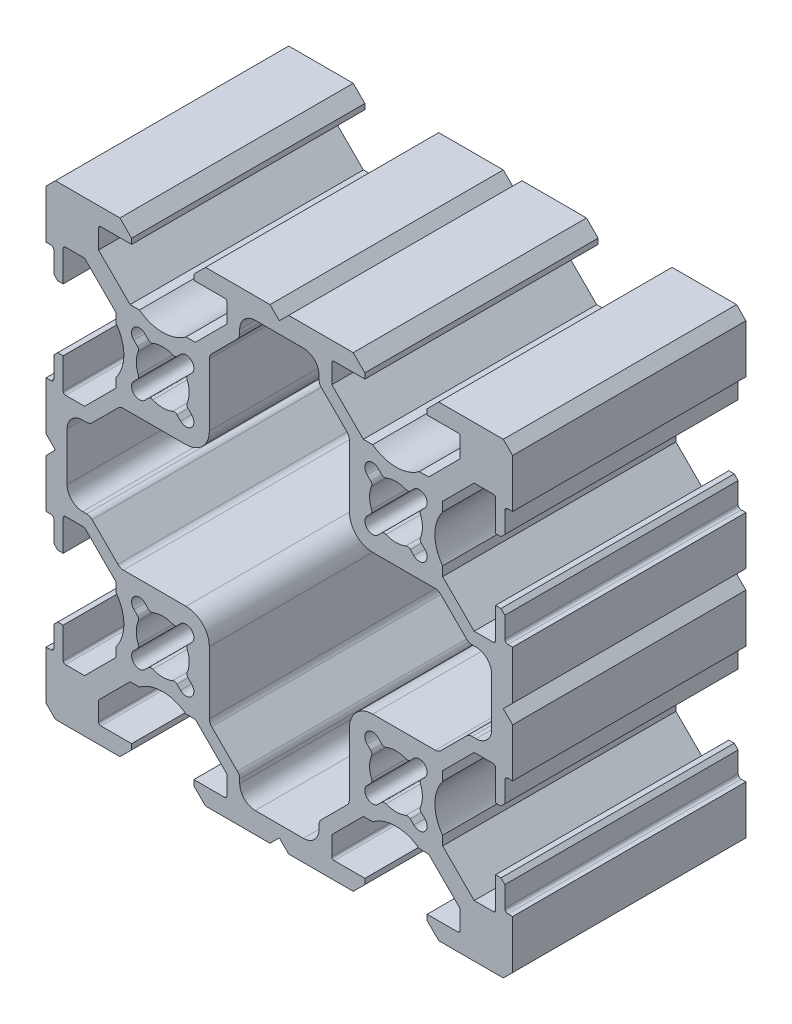
SolidWorks part; units mm, degrees
material "АД31Т ГОСТ 4784-97"
ref_plane "Спереди(Плоскость XY)" through (0, 0, 0) normal (0, 0, 1) x (1, 0, 0)
ref_plane "Сверху(Плоскость XZ)" through (0, 0, 0) normal (0, 1, 0) x (1, 0, 0)
ref_plane "Справа(Плоскость ZY)" through (0, 0, 0) normal (1, 0, 0) x (0, 0, -1)
sketch "Эскиз1" plane through (0, 0, 0) normal (0, 0, 1) x (1, 0, 0)
  line B0 (-19.6151, -16.8385) -> (-20.0747, -17.2981)
  line B1 (-20.0747, -12.7019) -> (-19.6151, -13.1615)
  line B2 (-18.2009, -11.7473) -> (-18.6605, -11.2877)
  line B3 (-14.0643, -11.2877) -> (-14.5239, -11.7473)
  line B4 (-13.1097, -13.1615) -> (-12.6501, -12.7019)
  line B5 (-12.6501, -17.2981) -> (-13.1097, -16.8385)
  line B6 (-14.5239, -18.2527) -> (-14.0643, -18.7123)
  line B7 (-18.6605, -18.7123) -> (-18.2009, -18.2527)
  line B8 (9.9253, -12.7019) -> (10.3849, -13.1615)
  line B9 (11.7991, -11.7473) -> (11.3395, -11.2877)
  line B10 (15.9357, -11.2877) -> (15.4761, -11.7473)
  line B11 (16.8903, -13.1615) -> (17.3499, -12.7019)
  line B12 (17.3499, -17.2981) -> (16.8903, -16.8385)
  line B13 (15.4761, -18.2527) -> (15.9357, -18.7123)
  line B14 (11.3395, -18.7123) -> (11.7991, -18.2527)
  line B15 (10.3849, -16.8385) -> (9.9253, -17.2981)
  line B16 (10.3849, 13.1615) -> (9.9253, 12.7019)
  line B17 (9.9253, 17.2981) -> (10.3849, 16.8385)
  line B18 (11.7991, 18.2527) -> (11.3395, 18.7123)
  line B19 (15.9357, 18.7123) -> (15.4761, 18.2527)
  line B20 (16.8903, 16.8385) -> (17.3499, 17.2981)
  line B21 (17.3499, 12.7019) -> (16.8903, 13.1615)
  line B22 (15.4761, 11.7473) -> (15.9357, 11.2877)
  line B23 (11.3395, 11.2877) -> (11.7991, 11.7473)
  line B24 (-18.2009, 18.2527) -> (-18.6605, 18.7123)
  line B25 (-14.0643, 18.7123) -> (-14.5239, 18.2527)
  line B26 (-13.1097, 16.8385) -> (-12.6501, 17.2981)
  line B27 (-12.6501, 12.7019) -> (-13.1097, 13.1615)
  line B28 (-14.5239, 11.7473) -> (-14.0643, 11.2877)
  line B29 (-18.6605, 11.2877) -> (-18.2009, 11.7473)
  line B30 (-19.6151, 13.1615) -> (-20.0747, 12.7019)
  line B31 (-20.0747, 17.2981) -> (-19.6151, 16.8385)
  line B32 (26.4376, 19) -> (27.1376, 19)
  line B33 (27.1376, 19) -> (27.6376, 19.5)
  line B34 (27.6376, 19.5) -> (27.6376, 22.15)
  line B35 (28.0376, 22.55) -> (28.6376, 22.55)
  line B36 (28.6376, 22.55) -> (28.6376, 28.8)
  line B37 (28.6376, 28.8) -> (27.4376, 30)
  line B38 (27.4376, 30) -> (19.1376, 30)
  line B39 (19.1376, 30) -> (17.6376, 28.5)
  line B40 (17.6376, 28.5) -> (17.6376, 27.8)
  line B41 (17.6376, 27.8) -> (21.5876, 27.8)
  line B42 (21.8876, 27.5) -> (21.8876, 25.0531)
  line B43 (21.8876, 25.0531) -> (17.8345, 21)
  line B44 (17.8345, 21) -> (16.6376, 21)
  line B45 (10.6376, 21) -> (9.4407, 21)
  line B46 (9.4407, 21) -> (5.3876, 25.0531)
  line B47 (5.3876, 25.0531) -> (5.3876, 27.5)
  line B48 (5.6876, 27.8) -> (9.6376, 27.8)
  line B49 (9.6376, 27.8) -> (9.6376, 28.5)
  line B50 (9.6376, 28.5) -> (8.1376, 30)
  line B51 (8.1376, 30) -> (-0.1624, 30)
  line B52 (-0.1624, 30) -> (-1.3624, 28.8)
  line B53 (-1.3624, 28.8) -> (-2.5624, 30)
  line B54 (-2.5624, 30) -> (-10.8624, 30)
  line B55 (-10.8624, 30) -> (-12.3624, 28.5)
  line B56 (-12.3624, 28.5) -> (-12.3624, 27.8)
  line B57 (-12.3624, 27.8) -> (-8.4124, 27.8)
  line B58 (-8.1124, 27.5) -> (-8.1124, 25.0531)
  line B59 (-8.1124, 25.0531) -> (-12.1655, 21)
  line B60 (-12.1655, 21) -> (-13.3624, 21)
  line B61 (-19.3624, 21) -> (-20.5593, 21)
  line B62 (-20.5593, 21) -> (-24.6124, 25.0531)
  line B63 (-24.6124, 25.0531) -> (-24.6124, 27.5)
  line B64 (-24.3124, 27.8) -> (-20.3624, 27.8)
  line B65 (-20.3624, 27.8) -> (-20.3624, 28.5)
  line B66 (-20.3624, 28.5) -> (-21.8624, 30)
  line B67 (-21.8624, 30) -> (-30.1624, 30)
  line B68 (-30.1624, 30) -> (-31.3624, 28.8)
  line B69 (-31.3624, 28.8) -> (-31.3624, 22.55)
  line B70 (-31.3624, 22.55) -> (-30.7624, 22.55)
  line B71 (-30.3624, 22.15) -> (-30.3624, 19.5)
  line B72 (-30.3624, 19.5) -> (-29.8624, 19)
  line B73 (-29.8624, 19) -> (-29.1624, 19)
  line B74 (-29.1624, 19) -> (-29.1624, 22.95)
  line B75 (-28.8624, 23.25) -> (-26.4155, 23.25)
  line B76 (-26.4155, 23.25) -> (-22.3624, 19.1969)
  line B77 (-22.3624, 19.1969) -> (-22.3624, 18)
  line B78 (-22.3624, 12) -> (-22.3624, 10.8031)
  line B79 (-22.3624, 10.8031) -> (-26.4155, 6.75)
  line B80 (-26.4155, 6.75) -> (-28.8624, 6.75)
  line B81 (-29.1624, 7.05) -> (-29.1624, 11)
  line B82 (-29.1624, 11) -> (-29.8624, 11)
  line B83 (-29.8624, 11) -> (-30.3624, 10.5)
  line B84 (-30.3624, 10.5) -> (-30.3624, 7.85)
  line B85 (-30.7624, 7.45) -> (-31.3624, 7.45)
  line B86 (-31.3624, 7.45) -> (-31.3624, 1.2)
  line B87 (-31.3624, 1.2) -> (-30.1624, 0)
  line B88 (-30.1624, 0) -> (-31.3624, -1.2)
  line B89 (-31.3624, -1.2) -> (-31.3624, -7.45)
  line B90 (-31.3624, -7.45) -> (-30.7624, -7.45)
  line B91 (-30.3624, -7.85) -> (-30.3624, -10.5)
  line B92 (-30.3624, -10.5) -> (-29.8624, -11)
  line B93 (-29.8624, -11) -> (-29.1624, -11)
  line B94 (-29.1624, -11) -> (-29.1624, -7.05)
  line B95 (-28.8624, -6.75) -> (-26.4155, -6.75)
  line B96 (-26.4155, -6.75) -> (-22.3624, -10.8031)
  line B97 (-22.3624, -10.8031) -> (-22.3624, -12)
  line B98 (-22.3624, -18) -> (-22.3624, -19.1969)
  line B99 (-22.3624, -19.1969) -> (-26.4155, -23.25)
  line B100 (-26.4155, -23.25) -> (-28.8624, -23.25)
  line B101 (-29.1624, -22.95) -> (-29.1624, -19)
  line B102 (-29.1624, -19) -> (-29.8624, -19)
  line B103 (-29.8624, -19) -> (-30.3624, -19.5)
  line B104 (-30.3624, -19.5) -> (-30.3624, -22.15)
  line B105 (-30.7624, -22.55) -> (-31.3624, -22.55)
  line B106 (-31.3624, -22.55) -> (-31.3624, -28.8)
  line B107 (-31.3624, -28.8) -> (-30.1624, -30)
  line B108 (-30.1624, -30) -> (-21.8624, -30)
  line B109 (-21.8624, -30) -> (-20.3624, -28.5)
  line B110 (-20.3624, -28.5) -> (-20.3624, -27.8)
  line B111 (-20.3624, -27.8) -> (-24.3124, -27.8)
  line B112 (-24.6124, -27.5) -> (-24.6124, -25.0531)
  line B113 (-24.6124, -25.0531) -> (-20.5593, -21)
  line B114 (-20.5593, -21) -> (-19.3624, -21)
  line B115 (-13.3624, -21) -> (-12.1655, -21)
  line B116 (-12.1655, -21) -> (-8.1124, -25.0531)
  line B117 (-8.1124, -25.0531) -> (-8.1124, -27.5)
  line B118 (-8.4124, -27.8) -> (-12.3624, -27.8)
  line B119 (-12.3624, -27.8) -> (-12.3624, -28.5)
  line B120 (-12.3624, -28.5) -> (-10.8624, -30)
  line B121 (-10.8624, -30) -> (-2.5624, -30)
  line B122 (-2.5624, -30) -> (-1.3624, -28.8)
  line B123 (-1.3624, -28.8) -> (-0.1624, -30)
  line B124 (-0.1624, -30) -> (8.1376, -30)
  line B125 (8.1376, -30) -> (9.6376, -28.5)
  line B126 (9.6376, -28.5) -> (9.6376, -27.8)
  line B127 (9.6376, -27.8) -> (5.6876, -27.8)
  line B128 (5.3876, -27.5) -> (5.3876, -25.0531)
  line B129 (5.3876, -25.0531) -> (9.4407, -21)
  line B130 (9.4407, -21) -> (10.6376, -21)
  line B131 (16.6376, -21) -> (17.8345, -21)
  line B132 (17.8345, -21) -> (21.8876, -25.0531)
  line B133 (21.8876, -25.0531) -> (21.8876, -27.5)
  line B134 (21.5876, -27.8) -> (17.6376, -27.8)
  line B135 (17.6376, -27.8) -> (17.6376, -28.5)
  line B136 (17.6376, -28.5) -> (19.1376, -30)
  line B137 (19.1376, -30) -> (27.4376, -30)
  line B138 (27.4376, -30) -> (28.6376, -28.8)
  line B139 (28.6376, -28.8) -> (28.6376, -22.55)
  line B140 (28.6376, -22.55) -> (28.0376, -22.55)
  line B141 (27.6376, -22.15) -> (27.6376, -19.5)
  line B142 (27.6376, -19.5) -> (27.1376, -19)
  line B143 (27.1376, -19) -> (26.4376, -19)
  line B144 (26.4376, -19) -> (26.4376, -22.95)
  line B145 (26.1376, -23.25) -> (23.6907, -23.25)
  line B146 (23.6907, -23.25) -> (19.6376, -19.1969)
  line B147 (19.6376, -19.1969) -> (19.6376, -18)
  line B148 (19.6376, -12) -> (19.6376, -10.8031)
  line B149 (19.6376, -10.8031) -> (23.6907, -6.75)
  line B150 (23.6907, -6.75) -> (26.1376, -6.75)
  line B151 (26.4376, -7.05) -> (26.4376, -11)
  line B152 (26.4376, -11) -> (27.1376, -11)
  line B153 (27.1376, -11) -> (27.6376, -10.5)
  line B154 (27.6376, -10.5) -> (27.6376, -7.85)
  line B155 (28.0376, -7.45) -> (28.6376, -7.45)
  line B156 (28.6376, -7.45) -> (28.6376, -1.2)
  line B157 (28.6376, -1.2) -> (27.4376, 0)
  line B158 (27.4376, 0) -> (28.6376, 1.2)
  line B159 (28.6376, 1.2) -> (28.6376, 7.45)
  line B160 (28.6376, 7.45) -> (28.0376, 7.45)
  line B161 (27.6376, 7.85) -> (27.6376, 10.5)
  line B162 (27.6376, 10.5) -> (27.1376, 11)
  line B163 (27.1376, 11) -> (26.4376, 11)
  line B164 (26.4376, 11) -> (26.4376, 7.05)
  line B165 (26.1376, 6.75) -> (23.6907, 6.75)
  line B166 (23.6907, 6.75) -> (19.6376, 10.8031)
  line B167 (19.6376, 10.8031) -> (19.6376, 12)
  line B168 (19.6376, 18) -> (19.6376, 19.1969)
  line B169 (19.6376, 19.1969) -> (23.6907, 23.25)
  line B170 (23.6907, 23.25) -> (26.1376, 23.25)
  line B171 (26.4376, 22.95) -> (26.4376, 19)
  line B172 (7.3447, 20.7626) -> (4.0305, 24.0768)
  line B173 (7.6454, 12.0049) -> (7.6376, 20.0564)
  line B174 (18.694, 9) -> (10.6425, 9.0078)
  line B175 (22.7144, 5.3929) -> (19.4002, 8.7071)
  line B176 (23.9376, 5.1) -> (23.4215, 5.1)
  line B177 (25.9376, -3.1) -> (25.9376, 3.1)
  line B178 (23.4215, -5.1) -> (23.9376, -5.1)
  line B179 (19.4002, -8.7071) -> (22.7144, -5.3929)
  line B180 (10.6425, -9.0078) -> (18.694, -9)
  line B181 (7.6376, -20.0564) -> (7.6454, -12.0049)
  line B182 (4.0305, -24.0768) -> (7.3447, -20.7626)
  line B183 (3.7376, -25.3) -> (3.7376, -24.7839)
  line B184 (-4.4624, -27.3) -> (1.7376, -27.3)
  line B185 (-6.4624, -24.7839) -> (-6.4624, -25.3)
  line B186 (-10.0695, -20.7626) -> (-6.7553, -24.0768)
  line B187 (-10.3702, -12.0049) -> (-10.3624, -20.0564)
  line B188 (-21.4188, -9) -> (-13.3673, -9.0078)
  line B189 (-25.4392, -5.3929) -> (-22.125, -8.7071)
  line B190 (-26.6624, -5.1) -> (-26.1463, -5.1)
  line B191 (-28.6624, 3.1) -> (-28.6624, -3.1)
  line B192 (-26.1463, 5.1) -> (-26.6624, 5.1)
  line B193 (-22.125, 8.7071) -> (-25.4392, 5.3929)
  line B194 (-13.3673, 9.0078) -> (-21.4188, 9)
  line B195 (-10.3624, 20.0564) -> (-10.3702, 12.0049)
  line B196 (-6.7553, 24.0768) -> (-10.0695, 20.7626)
  line B197 (-6.4624, 25.3) -> (-6.4624, 24.7839)
  line B198 (1.7376, 27.3) -> (-4.4624, 27.3)
  line B199 (3.7376, 24.7839) -> (3.7376, 25.3)
  arc B200 (28.0376, 22.55) -> (27.6376, 22.15) centre (28.0376, 22.15) ccw
  arc B201 (21.8876, 27.5) -> (21.5876, 27.8) centre (21.5876, 27.5) ccw
  arc B202 (10.6376, 21) -> (16.6376, 21) centre (13.6376, 25) ccw
  arc B203 (5.6876, 27.8) -> (5.3876, 27.5) centre (5.6876, 27.5) ccw
  arc B204 (-8.1124, 27.5) -> (-8.4124, 27.8) centre (-8.4124, 27.5) ccw
  arc B205 (-19.3624, 21) -> (-13.3624, 21) centre (-16.3624, 25) ccw
  arc B206 (-24.3124, 27.8) -> (-24.6124, 27.5) centre (-24.3124, 27.5) ccw
  arc B207 (-30.3624, 22.15) -> (-30.7624, 22.55) centre (-30.7624, 22.15) ccw
  arc B208 (-28.8624, 23.25) -> (-29.1624, 22.95) centre (-28.8624, 22.95) ccw
  arc B209 (-22.3624, 12) -> (-22.3624, 18) centre (-26.3624, 15) ccw
  arc B210 (-29.1624, 7.05) -> (-28.8624, 6.75) centre (-28.8624, 7.05) ccw
  arc B211 (-30.7624, 7.45) -> (-30.3624, 7.85) centre (-30.7624, 7.85) ccw
  arc B212 (-30.3624, -7.85) -> (-30.7624, -7.45) centre (-30.7624, -7.85) ccw
  arc B213 (-28.8624, -6.75) -> (-29.1624, -7.05) centre (-28.8624, -7.05) ccw
  arc B214 (-22.3624, -18) -> (-22.3624, -12) centre (-26.3624, -15) ccw
  arc B215 (-29.1624, -22.95) -> (-28.8624, -23.25) centre (-28.8624, -22.95) ccw
  arc B216 (-30.7624, -22.55) -> (-30.3624, -22.15) centre (-30.7624, -22.15) ccw
  arc B217 (-24.6124, -27.5) -> (-24.3124, -27.8) centre (-24.3124, -27.5) ccw
  arc B218 (-13.3624, -21) -> (-19.3624, -21) centre (-16.3624, -25) ccw
  arc B219 (-8.4124, -27.8) -> (-8.1124, -27.5) centre (-8.4124, -27.5) ccw
  arc B220 (5.3876, -27.5) -> (5.6876, -27.8) centre (5.6876, -27.5) ccw
  arc B221 (16.6376, -21) -> (10.6376, -21) centre (13.6376, -25) ccw
  arc B222 (21.5876, -27.8) -> (21.8876, -27.5) centre (21.5876, -27.5) ccw
  arc B223 (27.6376, -22.15) -> (28.0376, -22.55) centre (28.0376, -22.15) ccw
  arc B224 (26.1376, -23.25) -> (26.4376, -22.95) centre (26.1376, -22.95) ccw
  arc B225 (19.6376, -12) -> (19.6376, -18) centre (23.6376, -15) ccw
  arc B226 (26.4376, -7.05) -> (26.1376, -6.75) centre (26.1376, -7.05) ccw
  arc B227 (28.0376, -7.45) -> (27.6376, -7.85) centre (28.0376, -7.85) ccw
  arc B228 (27.6376, 7.85) -> (28.0376, 7.45) centre (28.0376, 7.85) ccw
  arc B229 (26.1376, 6.75) -> (26.4376, 7.05) centre (26.1376, 7.05) ccw
  arc B230 (19.6376, 18) -> (19.6376, 12) centre (23.6376, 15) ccw
  arc B231 (26.4376, 22.95) -> (26.1376, 23.25) centre (26.1376, 22.95) ccw
  arc B232 (-19.6151, -16.8385) -> (-19.5063, -16.2945) centre (-19.9686, -16.4849) ccw
  arc B233 (-19.5063, -13.7055) -> (-19.5063, -16.2945) centre (-16.3624, -15) ccw
  arc B234 (-19.5063, -13.7055) -> (-19.6151, -13.1615) centre (-19.9686, -13.5151) ccw
  arc B235 (-18.6605, -11.2877) -> (-20.0747, -12.7019) centre (-19.3676, -11.9948) ccw
  arc B236 (-18.2009, -11.7473) -> (-17.6569, -11.8561) centre (-17.8473, -11.3938) ccw
  arc B237 (-15.0678, -11.8561) -> (-17.6569, -11.8561) centre (-16.3624, -15) ccw
  arc B238 (-15.0678, -11.8561) -> (-14.5239, -11.7473) centre (-14.8775, -11.3938) ccw
  arc B239 (-12.6501, -12.7019) -> (-14.0643, -11.2877) centre (-13.3572, -11.9948) ccw
  arc B240 (-13.1097, -13.1615) -> (-13.2185, -13.7055) centre (-12.7561, -13.5151) ccw
  arc B241 (-13.2185, -16.2945) -> (-13.2185, -13.7055) centre (-16.3624, -15) ccw
  arc B242 (-13.2185, -16.2945) -> (-13.1097, -16.8385) centre (-12.7561, -16.4849) ccw
  arc B243 (-14.0643, -18.7123) -> (-12.6501, -17.2981) centre (-13.3572, -18.0052) ccw
  arc B244 (-14.5239, -18.2527) -> (-15.0678, -18.1439) centre (-14.8775, -18.6062) ccw
  arc B245 (-17.6569, -18.1439) -> (-15.0678, -18.1439) centre (-16.3624, -15) ccw
  arc B246 (-17.6569, -18.1439) -> (-18.2009, -18.2527) centre (-17.8473, -18.6062) ccw
  arc B247 (-20.0747, -17.2981) -> (-18.6605, -18.7123) centre (-19.3676, -18.0052) ccw
  arc B248 (11.3395, -11.2877) -> (9.9253, -12.7019) centre (10.6324, -11.9948) ccw
  arc B249 (11.7991, -11.7473) -> (12.3431, -11.8561) centre (12.1527, -11.3938) ccw
  arc B250 (14.9322, -11.8561) -> (12.3431, -11.8561) centre (13.6376, -15) ccw
  arc B251 (14.9322, -11.8561) -> (15.4761, -11.7473) centre (15.1225, -11.3938) ccw
  arc B252 (17.3499, -12.7019) -> (15.9357, -11.2877) centre (16.6428, -11.9948) ccw
  arc B253 (16.8903, -13.1615) -> (16.7815, -13.7055) centre (17.2439, -13.5151) ccw
  arc B254 (16.7815, -16.2945) -> (16.7815, -13.7055) centre (13.6376, -15) ccw
  arc B255 (16.7815, -16.2945) -> (16.8903, -16.8385) centre (17.2439, -16.4849) ccw
  arc B256 (15.9357, -18.7123) -> (17.3499, -17.2981) centre (16.6428, -18.0052) ccw
  arc B257 (15.4761, -18.2527) -> (14.9322, -18.1439) centre (15.1225, -18.6062) ccw
  arc B258 (12.3431, -18.1439) -> (14.9322, -18.1439) centre (13.6376, -15) ccw
  arc B259 (12.3431, -18.1439) -> (11.7991, -18.2527) centre (12.1527, -18.6062) ccw
  arc B260 (9.9253, -17.2981) -> (11.3395, -18.7123) centre (10.6324, -18.0052) ccw
  arc B261 (10.3849, -16.8385) -> (10.4937, -16.2945) centre (10.0314, -16.4849) ccw
  arc B262 (10.4937, -13.7055) -> (10.4937, -16.2945) centre (13.6376, -15) ccw
  arc B263 (10.4937, -13.7055) -> (10.3849, -13.1615) centre (10.0314, -13.5151) ccw
  arc B264 (10.3849, 13.1615) -> (10.4937, 13.7055) centre (10.0314, 13.5151) ccw
  arc B265 (10.4937, 16.2945) -> (10.4937, 13.7055) centre (13.6376, 15) ccw
  arc B266 (10.4937, 16.2945) -> (10.3849, 16.8385) centre (10.0314, 16.4849) ccw
  arc B267 (11.3395, 18.7123) -> (9.9253, 17.2981) centre (10.6324, 18.0052) ccw
  arc B268 (11.7991, 18.2527) -> (12.3431, 18.1439) centre (12.1527, 18.6062) ccw
  arc B269 (14.9322, 18.1439) -> (12.3431, 18.1439) centre (13.6376, 15) ccw
  arc B270 (14.9322, 18.1439) -> (15.4761, 18.2527) centre (15.1225, 18.6062) ccw
  arc B271 (17.3499, 17.2981) -> (15.9357, 18.7123) centre (16.6428, 18.0052) ccw
  arc B272 (16.8903, 16.8385) -> (16.7815, 16.2945) centre (17.2439, 16.4849) ccw
  arc B273 (16.7815, 13.7055) -> (16.7815, 16.2945) centre (13.6376, 15) ccw
  arc B274 (16.7815, 13.7055) -> (16.8903, 13.1615) centre (17.2439, 13.5151) ccw
  arc B275 (15.9357, 11.2877) -> (17.3499, 12.7019) centre (16.6428, 11.9948) ccw
  arc B276 (15.4761, 11.7473) -> (14.9322, 11.8561) centre (15.1225, 11.3938) ccw
  arc B277 (12.3431, 11.8561) -> (14.9322, 11.8561) centre (13.6376, 15) ccw
  arc B278 (12.3431, 11.8561) -> (11.7991, 11.7473) centre (12.1527, 11.3938) ccw
  arc B279 (9.9253, 12.7019) -> (11.3395, 11.2877) centre (10.6324, 11.9948) ccw
  arc B280 (7.6376, 20.0564) -> (7.3447, 20.7626) centre (6.6376, 20.0555) ccw
  arc B281 (7.6454, 12.0049) -> (10.6425, 9.0078) centre (10.6454, 12.0078) ccw
  arc B282 (19.4002, 8.7071) -> (18.694, 9) centre (18.6931, 8) ccw
  arc B283 (22.7144, 5.3929) -> (23.4215, 5.1) centre (23.4215, 6.1) ccw
  arc B284 (25.9376, 3.1) -> (23.9376, 5.1) centre (23.9376, 3.1) ccw
  arc B285 (23.9376, -5.1) -> (25.9376, -3.1) centre (23.9376, -3.1) ccw
  arc B286 (23.4215, -5.1) -> (22.7144, -5.3929) centre (23.4215, -6.1) ccw
  arc B287 (18.694, -9) -> (19.4002, -8.7071) centre (18.6931, -8) ccw
  arc B288 (10.6425, -9.0078) -> (7.6454, -12.0049) centre (10.6454, -12.0078) ccw
  arc B289 (7.3447, -20.7626) -> (7.6376, -20.0564) centre (6.6376, -20.0555) ccw
  arc B290 (4.0305, -24.0768) -> (3.7376, -24.7839) centre (4.7376, -24.7839) ccw
  arc B291 (1.7376, -27.3) -> (3.7376, -25.3) centre (1.7376, -25.3) ccw
  arc B292 (-6.4624, -25.3) -> (-4.4624, -27.3) centre (-4.4624, -25.3) ccw
  arc B293 (-6.4624, -24.7839) -> (-6.7553, -24.0768) centre (-7.4624, -24.7839) ccw
  arc B294 (-10.3624, -20.0564) -> (-10.0695, -20.7626) centre (-9.3624, -20.0555) ccw
  arc B295 (-10.3702, -12.0049) -> (-13.3673, -9.0078) centre (-13.3702, -12.0078) ccw
  arc B296 (-22.125, -8.7071) -> (-21.4188, -9) centre (-21.4178, -8) ccw
  arc B297 (-25.4392, -5.3929) -> (-26.1463, -5.1) centre (-26.1463, -6.1) ccw
  arc B298 (-28.6624, -3.1) -> (-26.6624, -5.1) centre (-26.6624, -3.1) ccw
  arc B299 (-26.6624, 5.1) -> (-28.6624, 3.1) centre (-26.6624, 3.1) ccw
  arc B300 (-26.1463, 5.1) -> (-25.4392, 5.3929) centre (-26.1463, 6.1) ccw
  arc B301 (-21.4188, 9) -> (-22.125, 8.7071) centre (-21.4178, 8) ccw
  arc B302 (-13.3673, 9.0078) -> (-10.3702, 12.0049) centre (-13.3702, 12.0078) ccw
  arc B303 (-10.0695, 20.7626) -> (-10.3624, 20.0564) centre (-9.3624, 20.0555) ccw
  arc B304 (-6.7553, 24.0768) -> (-6.4624, 24.7839) centre (-7.4624, 24.7839) ccw
  arc B305 (-4.4624, 27.3) -> (-6.4624, 25.3) centre (-4.4624, 25.3) ccw
  arc B306 (3.7376, 25.3) -> (1.7376, 27.3) centre (1.7376, 25.3) ccw
  arc B307 (3.7376, 24.7839) -> (4.0305, 24.0768) centre (4.7376, 24.7839) ccw
  arc B308 (-18.2009, 18.2527) -> (-17.6569, 18.1439) centre (-17.8473, 18.6062) ccw
  arc B309 (-15.0678, 18.1439) -> (-17.6569, 18.1439) centre (-16.3624, 15) ccw
  arc B310 (-15.0678, 18.1439) -> (-14.5239, 18.2527) centre (-14.8775, 18.6062) ccw
  arc B311 (-12.6501, 17.2981) -> (-14.0643, 18.7123) centre (-13.3572, 18.0052) ccw
  arc B312 (-13.1097, 16.8385) -> (-13.2185, 16.2945) centre (-12.7561, 16.4849) ccw
  arc B313 (-13.2185, 13.7055) -> (-13.2185, 16.2945) centre (-16.3624, 15) ccw
  arc B314 (-13.2185, 13.7055) -> (-13.1097, 13.1615) centre (-12.7561, 13.5151) ccw
  arc B315 (-14.0643, 11.2877) -> (-12.6501, 12.7019) centre (-13.3572, 11.9948) ccw
  arc B316 (-14.5239, 11.7473) -> (-15.0678, 11.8561) centre (-14.8775, 11.3938) ccw
  arc B317 (-17.6569, 11.8561) -> (-15.0678, 11.8561) centre (-16.3624, 15) ccw
  arc B318 (-17.6569, 11.8561) -> (-18.2009, 11.7473) centre (-17.8473, 11.3938) ccw
  arc B319 (-20.0747, 12.7019) -> (-18.6605, 11.2877) centre (-19.3676, 11.9948) ccw
  arc B320 (-19.6151, 13.1615) -> (-19.5063, 13.7055) centre (-19.9686, 13.5151) ccw
  arc B321 (-19.5063, 16.2945) -> (-19.5063, 13.7055) centre (-16.3624, 15) ccw
  arc B322 (-19.5063, 16.2945) -> (-19.6151, 16.8385) centre (-19.9686, 16.4849) ccw
  arc B323 (-18.6605, 18.7123) -> (-20.0747, 17.2981) centre (-19.3676, 18.0052) ccw
sketch_block_instance "Блок-60х60-1"
sketch_block "Блок-60х60"
extrude "Бобышка-Вытянуть1" add sketch "Эскиз1" along normal blind 30
